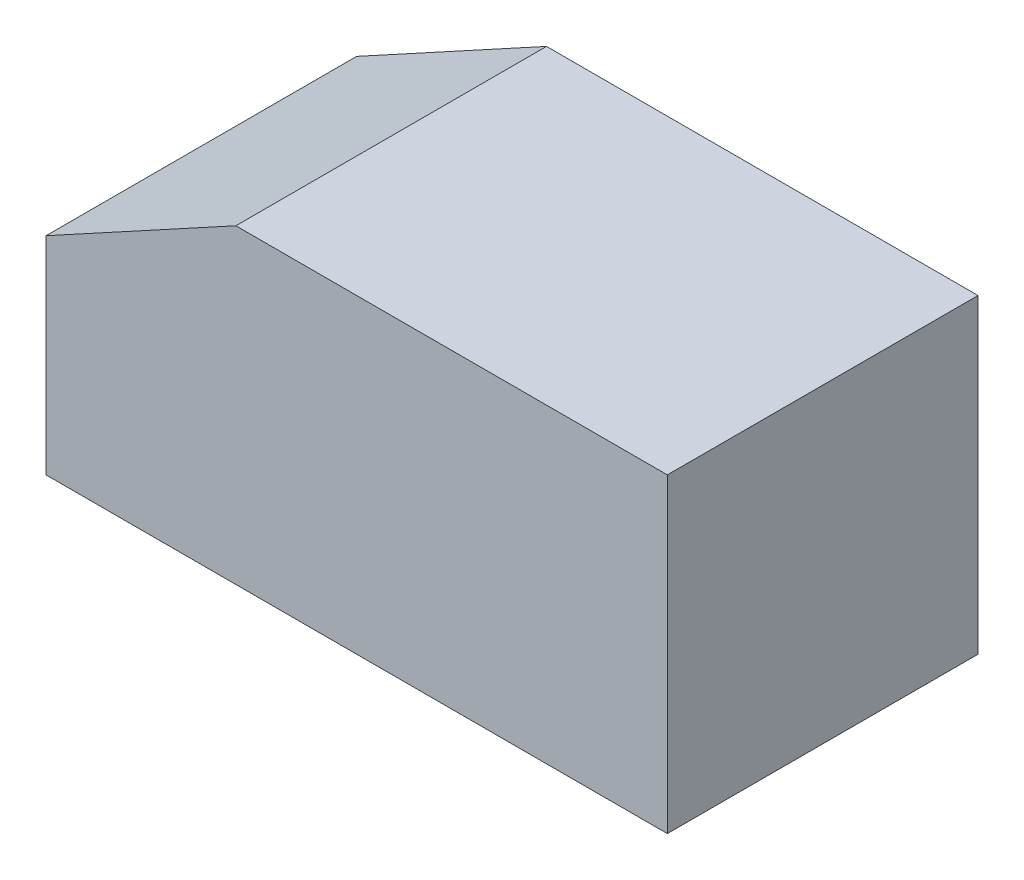
SolidWorks part; units mm, degrees
ref_plane "前视基准面" through (0, 0, 0) normal (0, 0, 1) x (1, 0, 0)
ref_plane "上视基准面" through (0, 0, 0) normal (0, 1, 0) x (1, 0, 0)
ref_plane "右视基准面" through (0, 0, 0) normal (1, 0, 0) x (0, 0, -1)
sketch "草图1" plane through (0, 0, 0) normal (0, 0, 1) x (1, 0, 0)
  line L0 (-31.5436, 3.673) -> (-31.5436, -8.327)
  line L1 (-31.5436, -8.327) -> (-1.5436, -8.327)
  line L2 (-1.5436, -8.327) -> (4.4564, -8.327)
  line L3 (4.4564, -8.327) -> (4.4564, 9.673)
  line L4 (4.4564, 9.673) -> (-20.5436, 9.673)
  line L5 (-20.5436, 9.673) -> (-31.5436, 3.673)
  dimension "D1" = 12
  dimension "D2" = 30
  dimension "D3" = 6
  dimension "D4" = 18
extrude "凸台-拉伸1" add sketch "草图1" along normal blind 18
